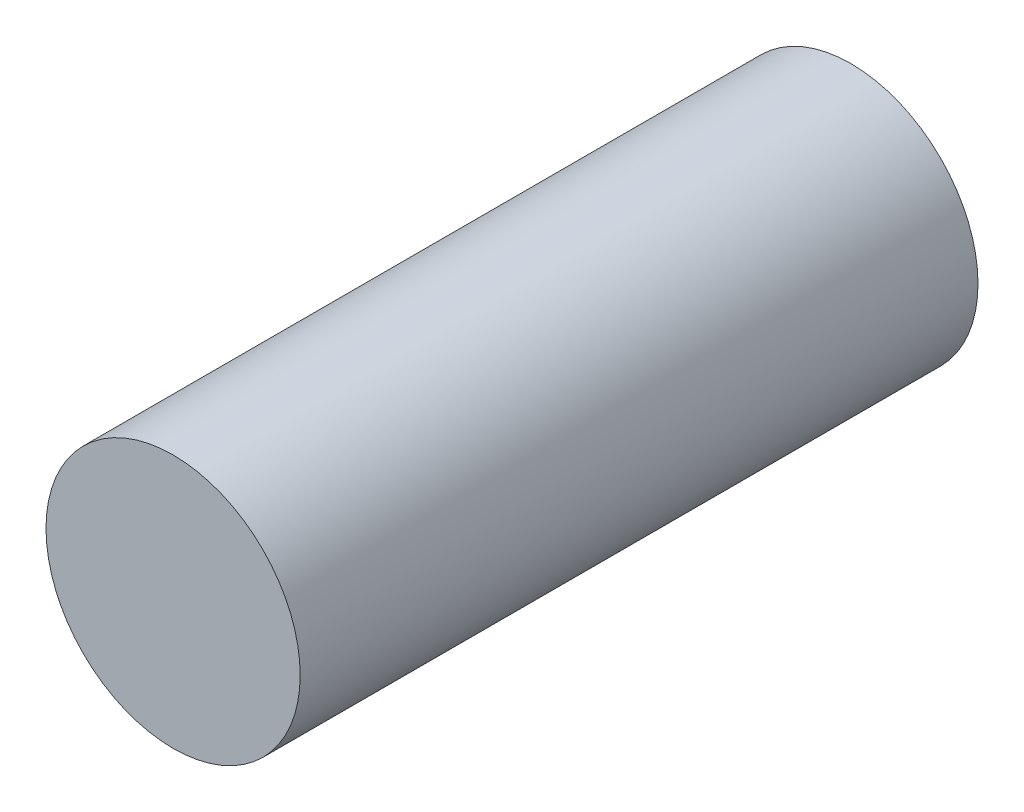
SolidWorks part; units mm, degrees
ref_plane "Alzado" through (0, 0, 0) normal (0, 0, 1) x (1, 0, 0)
ref_plane "Planta" through (0, 0, 0) normal (0, 1, 0) x (1, 0, 0)
ref_plane "Vista lateral" through (0, 0, 0) normal (1, 0, 0) x (0, 0, -1)
sketch "Croquis1" plane through (0, 0, 0) normal (0, 0, 1) x (1, 0, 0)
  circle A0 centre (0, 0) radius 10.5
  dimension "D1" = 21
extrude "Saliente-Extruir1" add sketch "Croquis1" along normal blind 56
